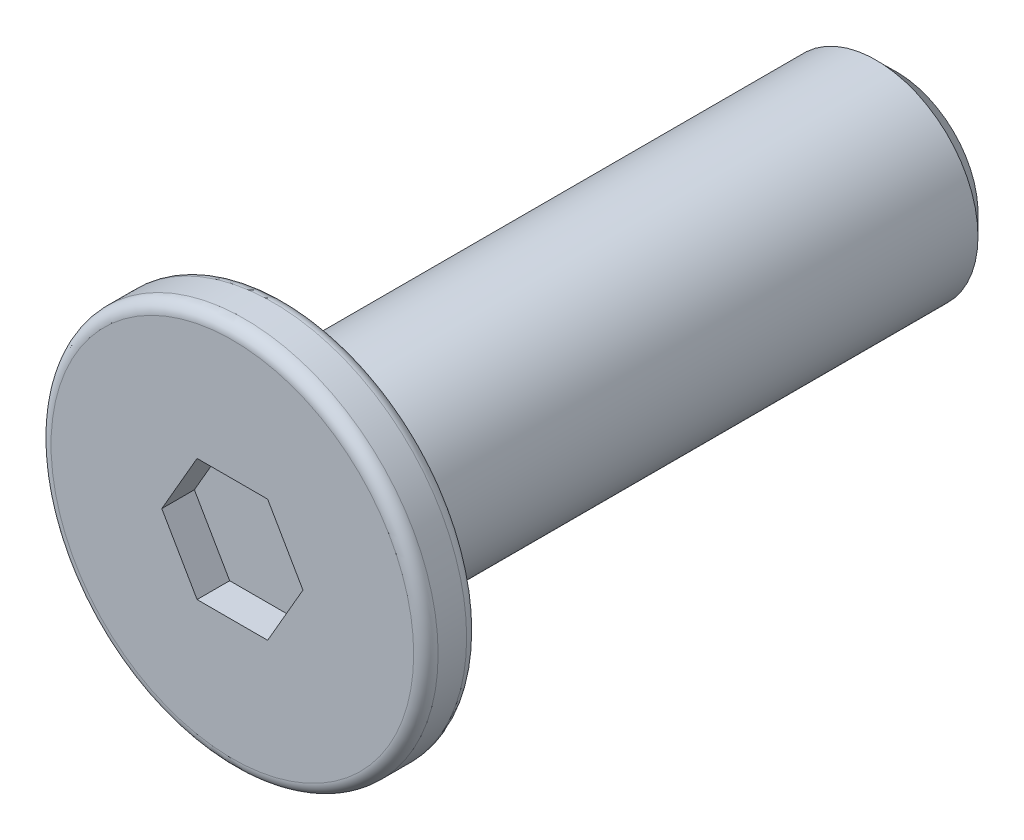
SolidWorks part; units mm, degrees
ref_plane "前视基准面" through (0, 0, 0) normal (0, 0, 1) x (1, 0, 0)
ref_plane "上视基准面" through (0, 0, 0) normal (0, 1, 0) x (1, 0, 0)
ref_plane "右视基准面" through (0, 0, 0) normal (1, 0, 0) x (0, 0, -1)
sketch "草图1" plane through (0, 0, 0) normal (0, 0, 1) x (1, 0, 0)
  circle A0 centre (0, 0) radius 4.75
  dimension "D1" = 9.5
extrude "凸台-拉伸1" add sketch "草图1" along normal mid plane 1.3
sketch "草图2" plane through (0, 0, -0.65) normal (0, 0, -1) x (-1, 0, 0)
  circle A0 centre (0, 0) radius 2.5
  dimension "D1" = 5
extrude "凸台-拉伸2" add sketch "草图2" along normal blind 15
chamfer "倒角1" distance 0.5 angle 45 1 edges at (-2.5, 0, -15.65)
sketch "草图3" plane through (0, 0, 0.65) normal (0, 0, 1) x (1, 0, 0)
  line L1 (1.7321, 0) -> (0.866, 1.5)
  line L2 (0.866, 1.5) -> (-0.866, 1.5)
  line L3 (-0.866, 1.5) -> (-1.7321, 0)
  line L4 (-1.7321, 0) -> (-0.866, -1.5)
  line L5 (-0.866, -1.5) -> (0.866, -1.5)
  line L6 (0.866, -1.5) -> (1.7321, 0)
  circle A0 centre (0, 0) radius 1.5 construction
  dimension "D1" = 3
extrude "切除-拉伸1" cut sketch "草图3" against normal blind 0.8
fillet "圆角2" radius 0.3 2 edges at (4.75, 0, -0.65) (4.75, 0, 0.65)
